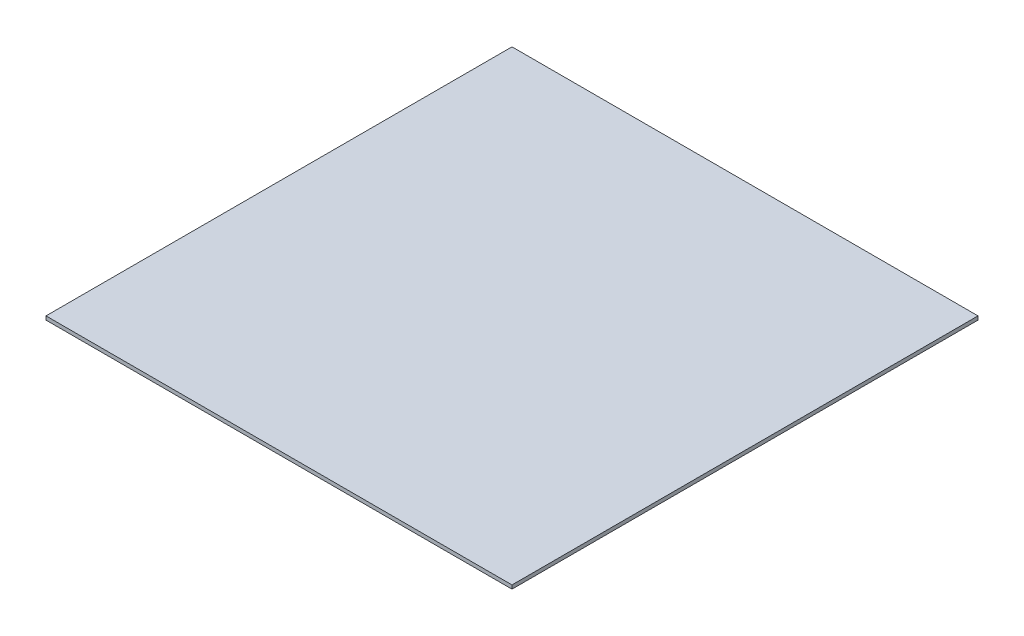
SolidWorks part; units mm, degrees
ref_plane "Plan de face" through (0, 0, 0) normal (0, 0, 1) x (1, 0, 0)
ref_plane "Plan de dessus" through (0, 0, 0) normal (0, 1, 0) x (1, 0, 0)
ref_plane "Plan de droite" through (0, 0, 0) normal (1, 0, 0) x (0, 0, -1)
sketch "Esquisse1" plane through (0, 0, 0) normal (0, 1, 0) x (1, 0, 0)
  line L1 (-252.5, -252.5) -> (252.5, -252.5)
  line L2 (-252.5, -252.5) -> (-252.5, 252.5)
  line L3 (-252.5, 252.5) -> (252.5, 252.5)
  line L4 (252.5, -252.5) -> (252.5, 252.5)
  line L5 (-252.5, -252.5) -> (252.5, 252.5) construction
  line L6 (-252.5, 252.5) -> (252.5, -252.5) construction
  point P0 (0, 0)
  dimension "D1" = 505
extrude "Boss.-Extru.1" add sketch "Esquisse1" along normal blind 4
